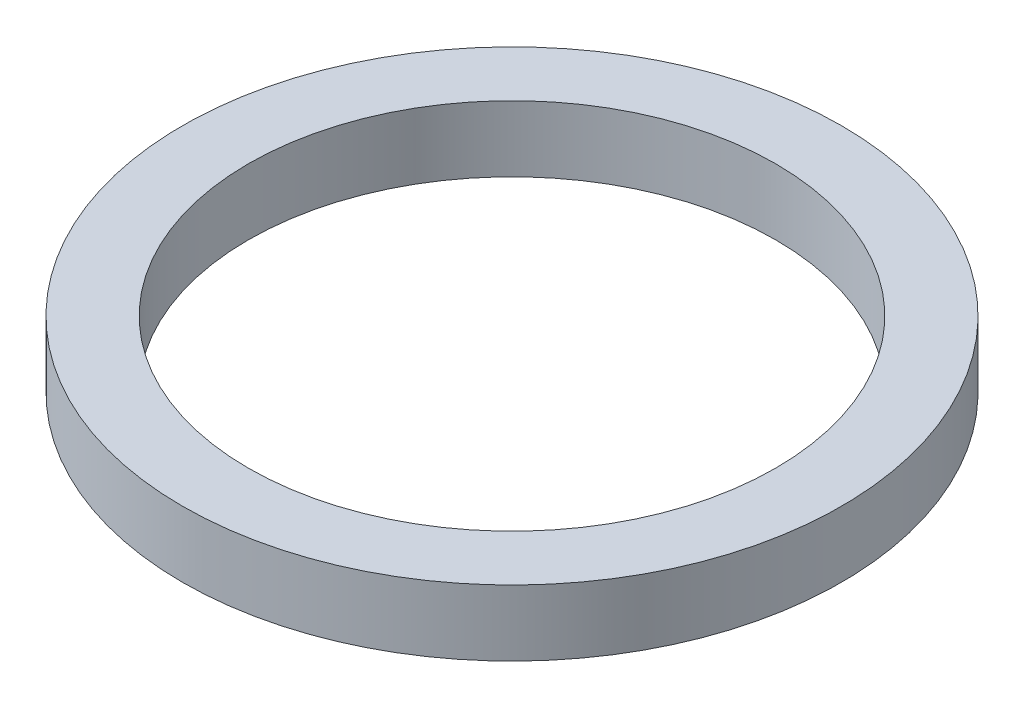
SolidWorks part; units mm, degrees
material "C (Graphite)"
ref_plane "Front Plane" through (0, 0, 0) normal (0, 0, 1) x (1, 0, 0)
ref_plane "Top Plane" through (0, 0, 0) normal (0, 1, 0) x (1, 0, 0)
ref_plane "Right Plane" through (0, 0, 0) normal (1, 0, 0) x (0, 0, -1)
sketch "Sketch1" plane through (0, 0, 0) normal (0, 1, 0) x (1, 0, 0)
  circle A0 centre (0, 0) radius 12.7
  circle A1 centre (0, 0) radius 15.875
  dimension "D1" = 31.75
  dimension "D2" = 25.4
extrude "Boss-Extrude1" add sketch "Sketch1" along normal blind 3.175
